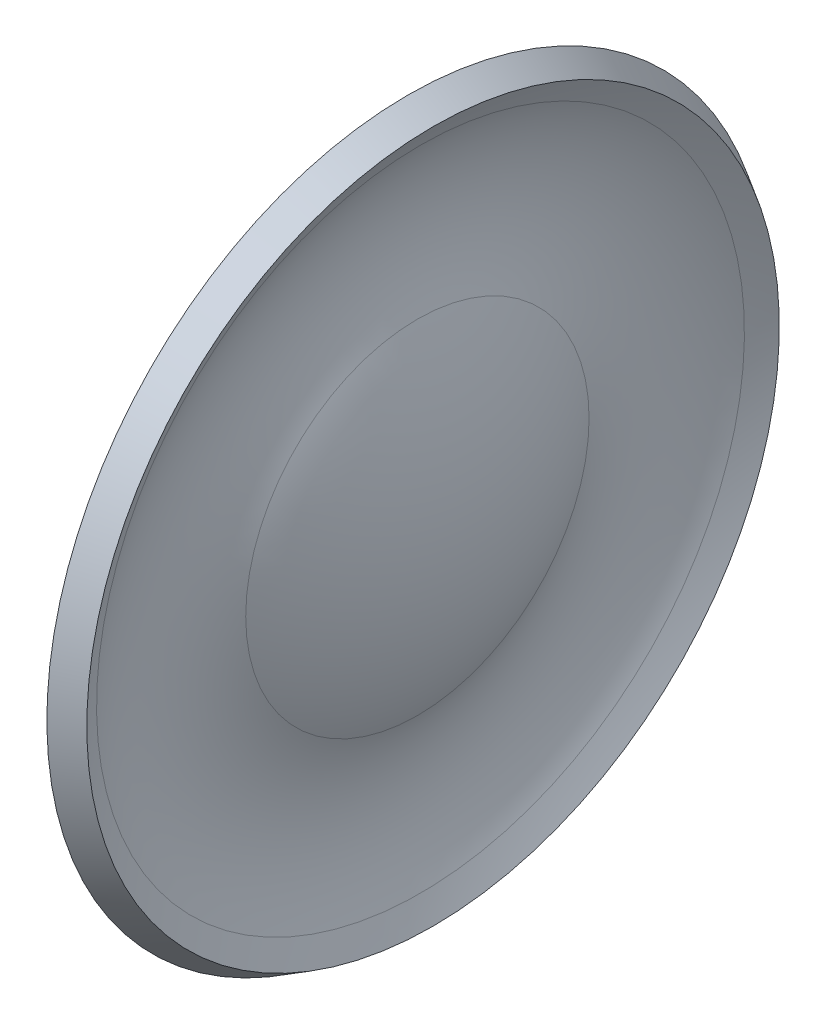
SolidWorks part; units mm, degrees
ref_plane "Front" through (0, 0, 0) normal (0, 0, 1) x (1, 0, 0)
ref_plane "Top" through (0, 0, 0) normal (0, 1, 0) x (1, 0, 0)
ref_plane "Right" through (0, 0, 0) normal (1, 0, 0) x (0, 0, -1)
sketch "Sketch1" plane through (0, 0, 0) normal (0, 0, 1) x (1, 0, 0)
  line L0 (-6.4155, 3.7719) -> (-6.4155, 3.1574) construction
  line L1 (0, 0) -> (-7.4422, 0) construction
  line L2 (-7.4422, 0) -> (-7.1374, 0)
  line L3 (-6.4155, 3.7719) -> (-6.1528, 3.6174)
  arc A0 (-6.4155, 3.7719) -> (-7.4422, 0) centre (0, 0) ccw
  arc A1 (-6.1528, 3.6174) -> (-7.1374, 0) centre (0, 0) ccw
  dimension "D1" = 7.1374
  dimension "D2" = 0.3048
  dimension "D3" = 7.5438
revolve "Revolve1" [suppressed] add sketch "Sketch1" angle 360 about L1
sketch "Sketch2" plane through (0, 0, 0) normal (0, 0, 1) x (1, 0, 0)
  line L0 (0, 0) -> (-7.4422, 0) construction
  line L1 (0, 0) -> (-6.2073, 0) construction
  line L2 (-7.4422, 0) -> (-7.1374, 0)
  line L3 (-6.1528, 3.6174) -> (-6.4155, 3.7719)
  line L4 (-6.2073, 0) -> (-5.9025, 0)
  line L5 (-6.1528, 3.6174) -> (-6.4155, 3.7719)
  arc A0 (-5.9025, 0) -> (-6.3163, 1.7937) centre (-9.9967, 0) ccw
  arc A1 (-6.284, 3.3843) -> (-6.3163, 1.7937) centre (-4.7489, 2.5575) ccw
  arc A2 (-6.1528, 3.6174) -> (-7.1374, 0) centre (0, 0) ccw
  arc A3 (-6.4155, 3.7719) -> (-7.4422, 0) centre (0, 0) ccw
  arc A4 (-6.1528, 3.6174) -> (-6.284, 3.3843) centre (0, 0) ccw
  arc A5 (-6.4155, 3.7719) -> (-6.5524, 3.5288) centre (0, 0) ccw
  arc A6 (-6.2073, 0) -> (-6.5903, 1.6602) centre (-9.9967, 0) ccw
  arc A7 (-6.5524, 3.5288) -> (-6.5903, 1.6602) centre (-4.7489, 2.5575) ccw
  dimension "D2" = 9.9967
  dimension "D3" = 4.0942
  dimension "D4" = 4.7489
  dimension "D1" = 0
revolve "Revolve3" add sketch "Sketch2" angle 360 about L1
